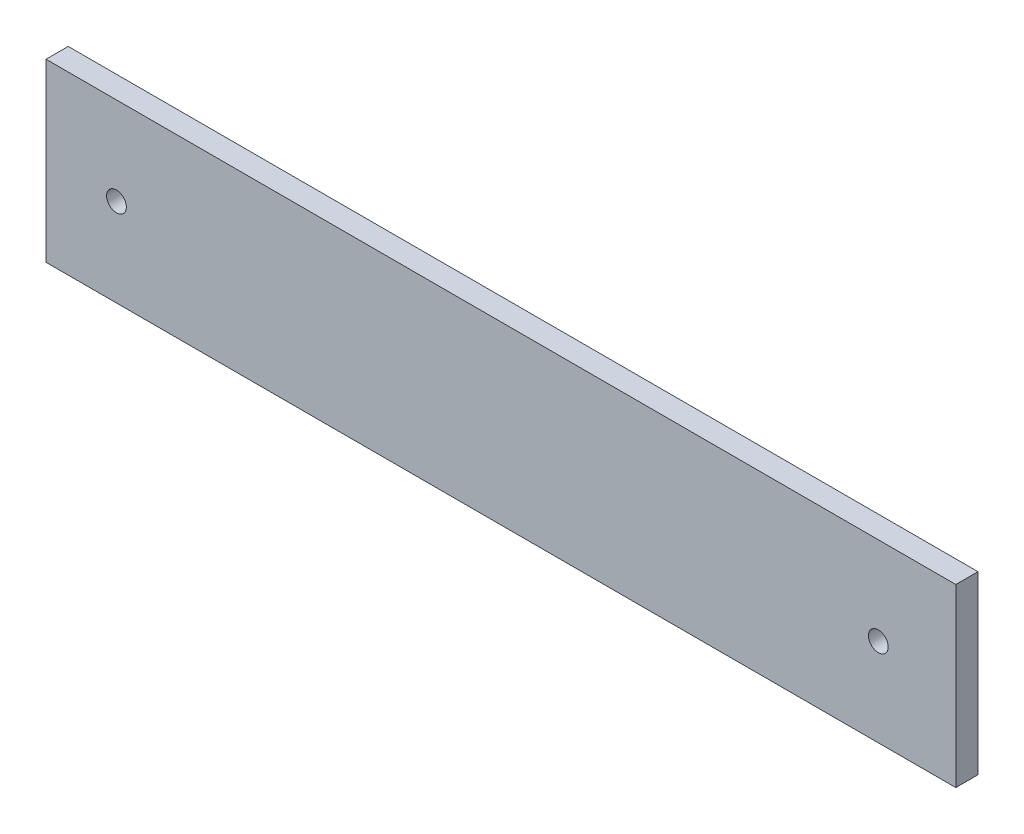
SolidWorks part; units mm, degrees
material "Maple"
ref_plane "Front Plane" through (0, 0, 0) normal (0, 0, 1) x (1, 0, 0)
ref_plane "Top Plane" through (0, 0, 0) normal (0, 1, 0) x (1, 0, 0)
ref_plane "Right Plane" through (0, 0, 0) normal (1, 0, 0) x (0, 0, -1)
sketch "Sketch1" plane through (0, 0, 0) normal (0, 0, 1) x (1, 0, 0)
  line L4 (70.7119, 14.4539) -> (70.7119, -10.7111)
  line L5 (-59.4588, 14.4539) -> (-59.4588, -10.7111)
  line L12 (-59.4588, -10.7111) -> (70.7119, -10.7111)
  line L15 (70.7119, 14.4539) -> (-59.4588, 14.4539)
  circle A0 centre (-49.375, 1.875) radius 1.415
  circle A1 centre (59.625, 1.875) radius 1.415
  dimension "D4" = 2.83
  dimension "D5" = 2.83
  dimension "D1" = 130.1706
  dimension "D2" = 25.165
  dimension "D3" = 109
extrude "Boss-Extrude1" add sketch "Sketch1" along normal blind 3.175
equation "\"rodr\"=25"
equation "\"rodrlength\"=130"
equation "\"rodrHole\"=2.83"
equation "\"D4@Sketch1\"=\"rodrHole\""
equation "\"D5@Sketch1\"=\"rodrHole\""
equation "\"rodrholedistance\"=10"
